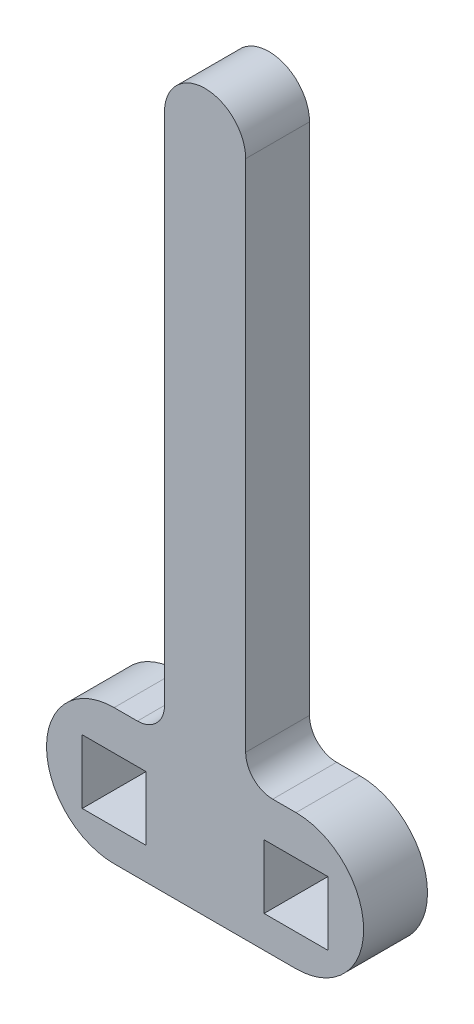
SolidWorks part; units mm, degrees
ref_plane "Front Plane" through (0, 0, 0) normal (0, 0, 1) x (1, 0, 0)
ref_plane "Top Plane" through (0, 0, 0) normal (0, 1, 0) x (1, 0, 0)
ref_plane "Right Plane" through (0, 0, 0) normal (1, 0, 0) x (0, 0, -1)
sketch "Sketch1" plane through (0, 0, 0) normal (0, 0, 1) x (1, 0, 0)
  line L0 (384.6105, 118.344) -> (367.5378, 118.344) construction
  line L1 (387.6077, 114.994) -> (381.6133, 114.994)
  line L2 (387.6077, 114.994) -> (387.6077, 120.9884)
  line L3 (387.6077, 120.9884) -> (381.6133, 120.9884)
  line L4 (381.6133, 114.994) -> (381.6133, 120.9884)
  line L5 (364.5406, 120.9884) -> (370.535, 120.9884)
  line L6 (364.5406, 120.9884) -> (364.5406, 114.994)
  line L7 (364.5406, 114.994) -> (370.535, 114.994)
  line L8 (370.535, 120.9884) -> (370.535, 114.994)
  line L9 (384.6105, 111.994) -> (367.5378, 111.994)
  line L10 (384.6105, 124.694) -> (382.4242, 124.694)
  line L11 (369.7242, 124.694) -> (367.5378, 124.694)
  line L12 (379.8842, 127.234) -> (379.8842, 175.494)
  line L13 (372.2642, 127.234) -> (372.2642, 175.494)
  arc A0 (384.6105, 111.994) -> (384.6105, 124.694) centre (384.6105, 118.344) ccw
  arc A1 (367.5378, 124.694) -> (367.5378, 111.994) centre (367.5378, 118.344) ccw
  arc A2 (379.8842, 175.494) -> (372.2642, 175.494) centre (376.0742, 175.494) ccw
  arc A3 (372.2642, 127.234) -> (369.7242, 124.694) centre (369.7242, 127.234) cw
  arc A4 (379.8842, 127.234) -> (382.4242, 124.694) centre (382.4242, 127.234) ccw
  point P10 (376.0742, 118.344)
  dimension "D1" = 2.54
  dimension "D2" = 2.54
extrude "Boss-Extrude1" add sketch "Sketch1" along normal blind 5.9944
